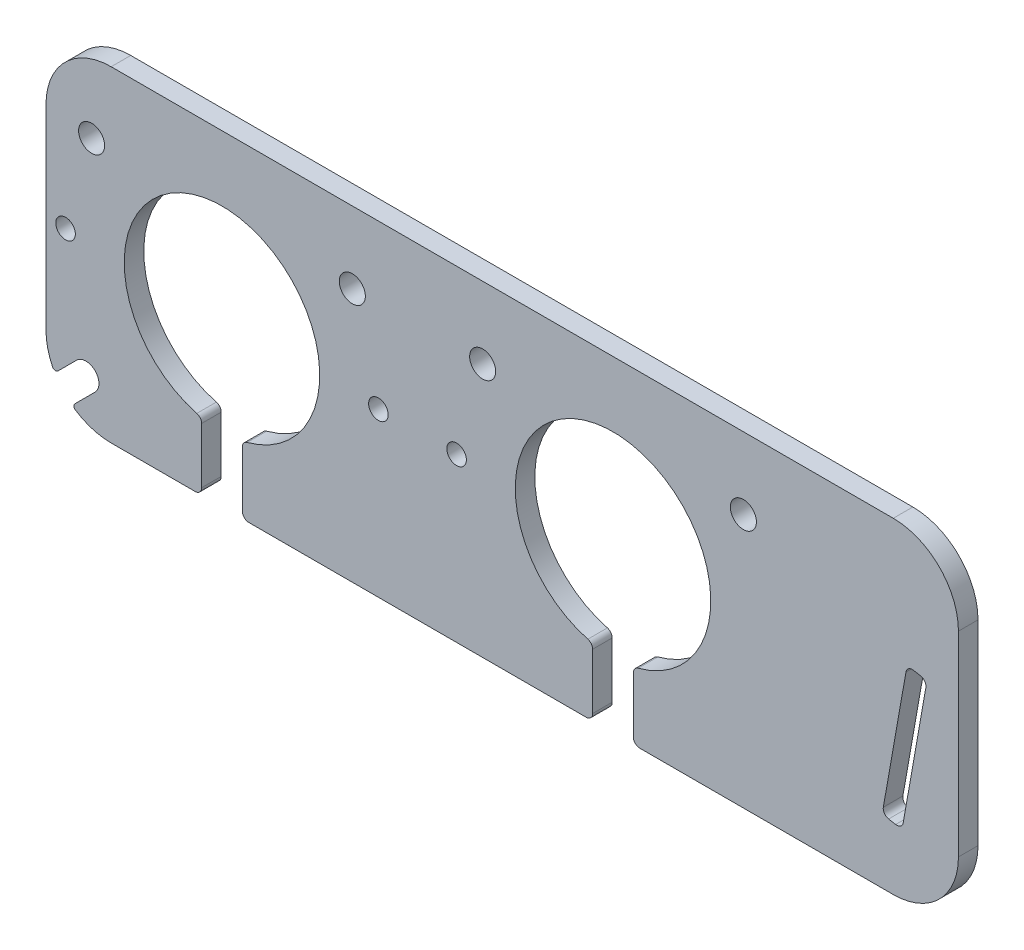
SolidWorks part; units mm, degrees
material "Plastique personnalisé"
ref_plane "Plan de face" through (0, 0, 0) normal (0, 0, 1) x (1, 0, 0)
ref_plane "Plan de dessus" through (0, 0, 0) normal (0, 1, 0) x (1, 0, 0)
ref_plane "Plan de droite" through (0, 0, 0) normal (1, 0, 0) x (0, 0, -1)
sketch "Esquisse1" plane through (0, 0, 0) normal (0, 0, 1) x (1, 0, 0)
  line L0 (-54, 25) -> (-6, 25) construction
  line L1 (-47, 50) -> (73, 50)
  line L2 (-49.4645, 5.5355) -> (-52.5797, 2.4203)
  line L3 (-47, 0) -> (-34.1196, 0)
  line L4 (0, 50) -> (0, 0) construction
  line L5 (54, 25) -> (6, 25) construction
  line L6 (83, 40) -> (83, 10)
  line L7 (73, 0) -> (47, 0)
  line L8 (10, 39) -> (50, 39) construction
  line L10 (-25.8804, 0) -> (25.8804, 0)
  line L11 (47, 0) -> (34.1196, 0)
  line L12 (-55.1817, 5.4752) -> (-52.2929, 8.364)
  line L13 (-57, 40) -> (-57, 10)
  line L14 (-33.1196, 9.5394) -> (-33.1196, 1)
  line L15 (26.8804, 9.5394) -> (26.8804, 1)
  line L16 (-26.8804, 9.5394) -> (-26.8804, 1)
  line L17 (33.1196, 9.5394) -> (33.1196, 1)
  line L18 (76.1056, 31.3495) -> (77.1888, 31.1585)
  line L19 (74.9471, 30.5383) -> (71.4741, 10.8422)
  line L20 (72.2853, 9.6837) -> (73.3686, 9.4927)
  line L21 (78, 30) -> (74.527, 10.3038)
  arc A0 (-25.8804, 0) -> (-26.8804, 1) centre (-25.8804, 1) cw
  circle A1 centre (-6, 25) radius 1.5
  circle A2 centre (-54, 25) radius 1.5
  arc A3 (73, 50) -> (83, 40) centre (73, 40) cw
  circle A4 centre (6, 25) radius 1.5
  arc A5 (83, 10) -> (73, 0) centre (73, 10) cw
  arc A6 (-52.5012, 1.6492) -> (-47, 0) centre (-47, 10) ccw
  arc A7 (71.4741, 10.8422) -> (72.2853, 9.6837) centre (72.4589, 10.6685) ccw
  arc A8 (73.3686, 9.4927) -> (74.527, 10.3038) centre (73.5422, 10.4775) ccw
  arc A9 (-47, 50) -> (-57, 40) centre (-47, 40) ccw
  circle A10 centre (50, 39) radius 2
  circle A11 centre (10, 39) radius 2
  circle A12 centre (-10, 39) radius 2
  circle A13 centre (-50, 39) radius 2
  arc A14 (-52.2929, 8.364) -> (-49.4645, 5.5355) centre (-50.8787, 6.9497) cw
  arc A15 (-55.9845, 5.6092) -> (-57, 10) centre (-47, 10) cw
  arc A16 (-52.5797, 2.4203) -> (-52.5012, 1.6492) centre (-52.2262, 2.0667) ccw
  arc A17 (76.1056, 31.3495) -> (74.9471, 30.5383) centre (75.9319, 30.3647) ccw
  arc A18 (77.1888, 31.1585) -> (78, 30) centre (77.0152, 30.1736) cw
  arc A20 (-55.1817, 5.4752) -> (-55.9845, 5.6092) centre (-55.5352, 5.8287) cw
  arc A22 (-33.8621, 10.5057) -> (-26.1379, 10.5057) centre (-30, 25) cw
  arc A23 (-26.1379, 10.5057) -> (-26.8804, 9.5394) centre (-25.8804, 9.5394) ccw
  arc A24 (-33.1196, 1) -> (-34.1196, 0) centre (-34.1196, 1) cw
  arc A25 (-33.8621, 10.5057) -> (-33.1196, 9.5394) centre (-34.1196, 9.5394) cw
  arc A26 (33.8621, 10.5057) -> (33.1196, 9.5394) centre (34.1196, 9.5394) ccw
  arc A27 (33.1196, 1) -> (34.1196, 0) centre (34.1196, 1) ccw
  arc A28 (26.1379, 10.5057) -> (26.8804, 9.5394) centre (25.8804, 9.5394) cw
  arc A29 (25.8804, 0) -> (26.8804, 1) centre (25.8804, 1) ccw
  arc A30 (33.8621, 10.5057) -> (26.1379, 10.5057) centre (30, 25) ccw
  point P44 (-53, 2)
  point P59 (-55.659, 4.9978)
  point P60 (75.1207, 31.5231)
  point P82 (78.1736, 30.9848)
  dimension "D2" = 3
  dimension "D3" = 3
  dimension "D5" = 10
  dimension "D10" = 1
  dimension "D11" = 4
  dimension "D19" = 0.5
  dimension "D6" = 1
  dimension "D4" = 10
  dimension "D7" = 24
  dimension "D8" = 30
  dimension "D9" = 3.1
  dimension "D12" = 40
  dimension "D13" = 10
  dimension "D14" = 22
  dimension "D15" = 4
  dimension "D16" = 140
  dimension "D17" = 45
  dimension "D18" = 5
  dimension "D20" = 10
  dimension "D21" = 5
  dimension "D22" = 20
extrude "Boss.-Extru.1" add sketch "Esquisse1" along normal blind 3
